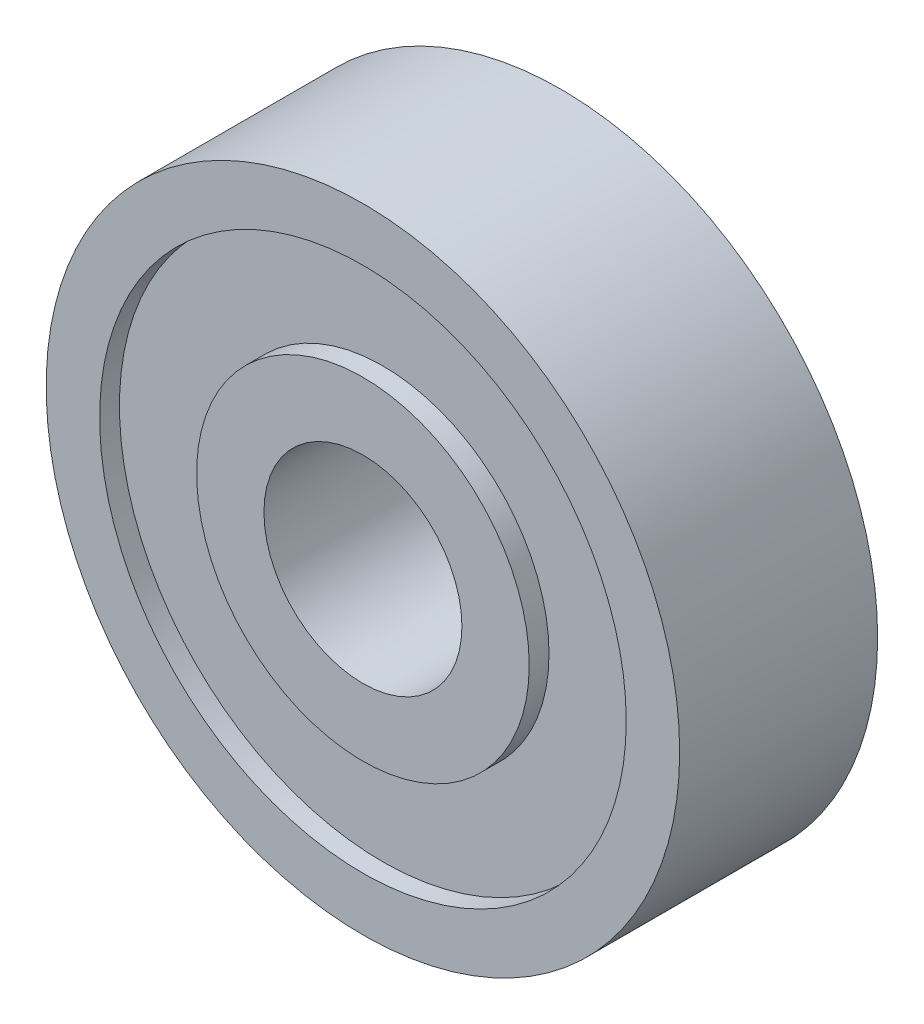
SolidWorks part; units mm, degrees
material "201 退火不鏽鋼 (SS)"
ref_plane "前基準面" through (0, 0, 0) normal (0, 0, 1) x (1, 0, 0)
ref_plane "上基準面" through (0, 0, 0) normal (0, 1, 0) x (1, 0, 0)
ref_plane "右基準面" through (0, 0, 0) normal (1, 0, 0) x (0, 0, -1)
sketch "草圖1" plane through (0, 0, 0) normal (0, 0, 1) x (1, 0, 0)
  circle A0 centre (0, 0) radius 8
  dimension "D1" = 16
extrude "填料-伸長1" add sketch "草圖1" along normal mid plane 5
sketch "草圖2" plane through (0, 0, 2.5) normal (0, 0, 1) x (1, 0, 0)
  circle A0 centre (0, 0) radius 2.5
  dimension "D1" = 5
extrude "除料-伸長1" cut sketch "草圖2" against normal through all
sketch "草圖3" plane through (0, 0, 2.5) normal (0, 0, 1) x (1, 0, 0)
  circle A0 centre (0, 0) radius 4.2
  circle A1 centre (0, 0) radius 6.65
  dimension "D1" = 13.3
  dimension "D2" = 8.4
extrude "除料-伸長2" cut sketch "草圖3" against normal blind 0.5
mirror "鏡射1" about plane through (0, 0, 0) normal (0, 0, 1) of "除料-伸長2"
